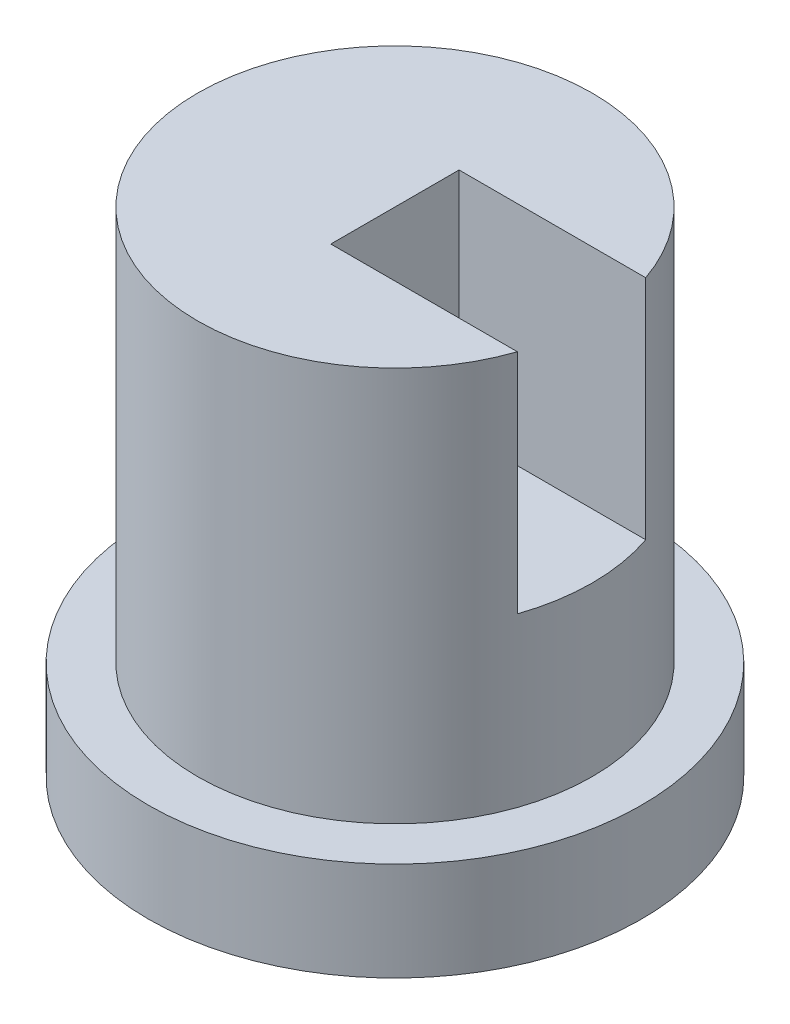
SolidWorks part; units mm, degrees
ref_plane "Alzado" through (0, 0, 0) normal (0, 0, 1) x (1, 0, 0)
ref_plane "Planta" through (0, 0, 0) normal (0, 1, 0) x (1, 0, 0)
ref_plane "Vista lateral" through (0, 0, 0) normal (1, 0, 0) x (0, 0, -1)
sketch "Croquis1" plane through (0, 0, 0) normal (0, 1, 0) x (1, 0, 0)
  circle A0 centre (0, 0) radius 25
  dimension "D1" = 50
extrude "Saliente-Extruir1" add sketch "Croquis1" along normal blind 10
sketch "Croquis2" plane through (0, 10, 0) normal (0, 1, 0) x (1, 0, 0)
  circle A1 centre (0, 0) radius 20
  point P0 (0, 0)
  dimension "D1" = 40
extrude "Saliente-Extruir3" add sketch "Croquis2" along normal blind 40 contours A1
sketch "Croquis4" plane through (0, 0, 0) normal (1, 0, 0) x (0, 0, -1)
  line L0 (20, 50) -> (-20, 50) construction
  line L1 (-6.5, 50) -> (6.5, 50)
  line L2 (-6.5, 50) -> (-6.5, 27)
  line L3 (-6.5, 27) -> (6.5, 27)
  line L4 (6.5, 50) -> (6.5, 27)
  line L5 (0, 0) -> (0, 27) construction
  line L6 (-25, 0) -> (25, 0) construction
  dimension "D1" = 13
  dimension "D2" = 23
extrude "Cortar-Extruir2" cut sketch "Croquis4" along normal blind 40
